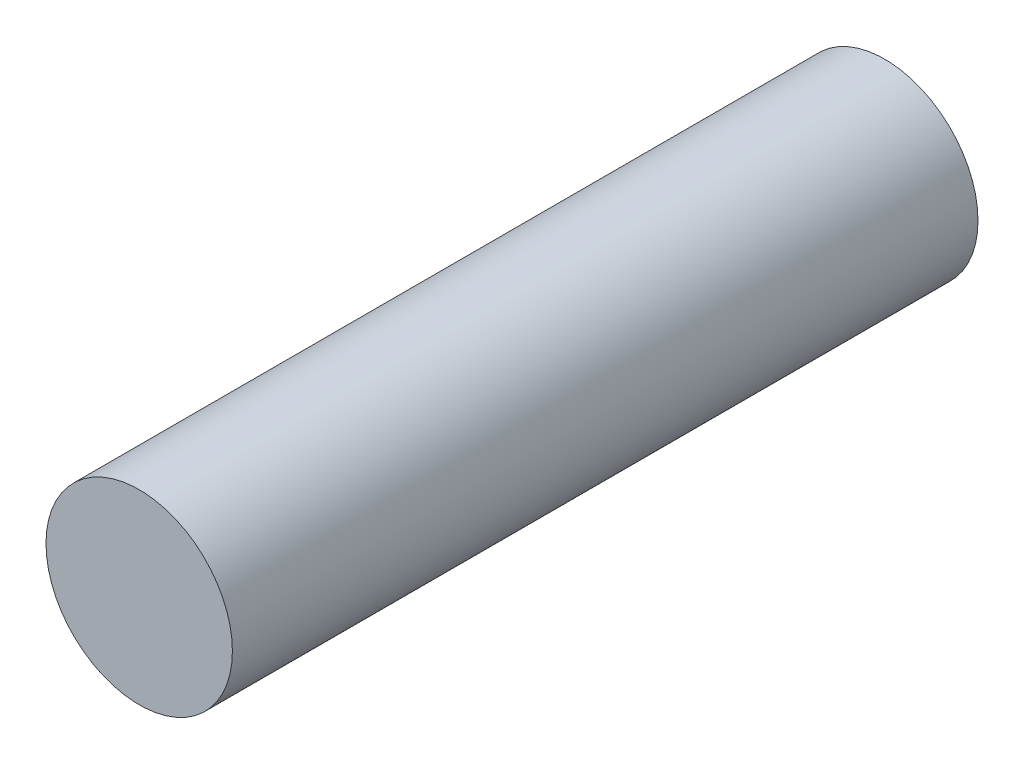
SolidWorks part; units mm, degrees
ref_plane "Plan de face" through (0, 0, 0) normal (0, 0, 1) x (1, 0, 0)
ref_plane "Plan de dessus" through (0, 0, 0) normal (0, 1, 0) x (1, 0, 0)
ref_plane "Plan de droite" through (0, 0, 0) normal (1, 0, 0) x (0, 0, -1)
sketch "Esquisse1" plane through (0, 0, 0) normal (0, 0, 1) x (1, 0, 0)
  circle A0 centre (0, 0) radius 0.5
  dimension "D1" = 1
extrude "Boss.-Extru.1" add sketch "Esquisse1" along normal blind 4
